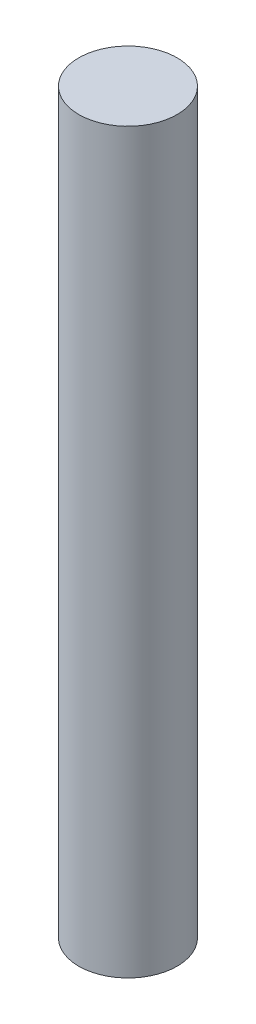
SolidWorks part; units mm, degrees
ref_plane "Front Plane" through (0, 0, 0) normal (0, 0, 1) x (1, 0, 0)
ref_plane "Top Plane" through (0, 0, 0) normal (0, 1, 0) x (1, 0, 0)
ref_plane "Right Plane" through (0, 0, 0) normal (1, 0, 0) x (0, 0, -1)
sketch "Sketch1" plane through (0, 0, 0) normal (0, 1, 0) x (1, 0, 0)
  circle A0 centre (0, 0) radius 5
  dimension "D1" = 10
extrude "Boss-Extrude1" add sketch "Sketch1" along normal mid plane 75
